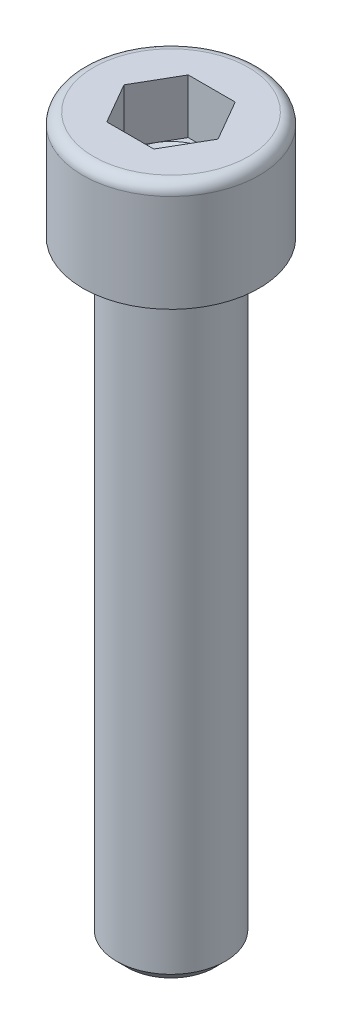
SolidWorks part; units mm, degrees
ref_plane "Plan1" through (0, 0, 0) normal (0, 0, 1) x (1, 0, 0)
ref_plane "Plan2" through (0, 0, 0) normal (0, 1, 0) x (1, 0, 0)
ref_plane "Plan3" through (0, 0, 0) normal (1, 0, 0) x (0, 0, -1)
sketch "Esquisse2" plane through (0, 0, 0) normal (0, 1, 0) x (1, 0, 0)
  circle A0 centre (0, 0) radius 4
  dimension "Diamètre nominal" = 8
extrude "Base-Extrusion" add sketch "Esquisse2" against normal blind 45
chamfer "Chanfrein1" distance 0.8 angle 45
sketch "Esquisse5" plane through (0, 0, 0) normal (0, 0, 1) x (1, 0, 0)
  line L0 (-10.25, 0) -> (2.75, 0) construction
  line L1 (3, 8) -> (3, 4)
  line L2 (0, 0) -> (6.5, 0)
  line L3 (0, 0) -> (0, 2.2679)
  line L4 (3, 8) -> (5.7, 8)
  line L5 (6.5, 0) -> (6.5, 7.2)
  line L6 (3, 4) -> (0, 2.2679)
  line L7 (0, 8) -> (0, -45) construction
  line L8 (0, -44.2) -> (0, 0) construction
  line L9 (-3.2, -45) -> (3.2, -45) construction
  line L10 (3, 0) -> (-3, 0) construction
  arc A0 (6.5, 7.2) -> (5.7, 8) centre (5.7, 7.2) ccw
  dimension "D2" = 0.8
  dimension "D1" = 6.5
  dimension "Cote sur plats" = 6
  dimension "D3" = 60
  dimension "D4" = 4
  dimension "Diamètre tête" = 13
  dimension "Diamètre nominal" = 8
  dimension "D5" = 3
revolve "Boss.-Révol.1" add sketch "Esquisse5" angle 360 about L7
sketch "Esquisse7" plane through (0, 8, 0) normal (0, 1, 0) x (-1, 0, 0)
  line L0 (0, -3) -> (0, 3) construction
  line L1 (0, 0) -> (-1.7321, 3) construction
  line L2 (0, 0) -> (-2.5981, 1.5) construction
  line L3 (0, 0) -> (-3.4641, 0) construction
  line L4 (1.7321, 3) -> (-1.7321, 3)
  line L5 (-1.7321, 3) -> (-3.4641, 0)
  line L6 (1.7321, -3) -> (-1.7321, -3)
  line L7 (-1.7321, -3) -> (-3.4641, 0)
  line L8 (1.7321, 3) -> (3.4641, 0)
  line L9 (1.7321, -3) -> (3.4641, 0)
  circle A2 centre (0, 0) radius 3 construction
  dimension "D1" = 30
  dimension "D2" = 30
extrude "Enlèv. mat.-Extru.1" cut sketch "Esquisse7" against normal blind 4
equation "\"D1@Chanfrein1\" = \"Diamètre nominal@Esquisse2\"*0.1"
equation "\"D1@Esquisse5\" = \"Diamètre tête@Esquisse5\"/2"
equation "\"D2@Esquisse5\" = \"Diamètre nominal@Esquisse5\"*0.1"
equation "\"D4@Esquisse5\" = \"Diamètre nominal@Esquisse5\"/2"
equation "\"D5@Esquisse5\" = \"Cote sur plats@Esquisse5\"/2"
equation "\"D1@Enlèv. mat.-Extru.1\" = \"Diamètre nominal@Esquisse5\"/2"
